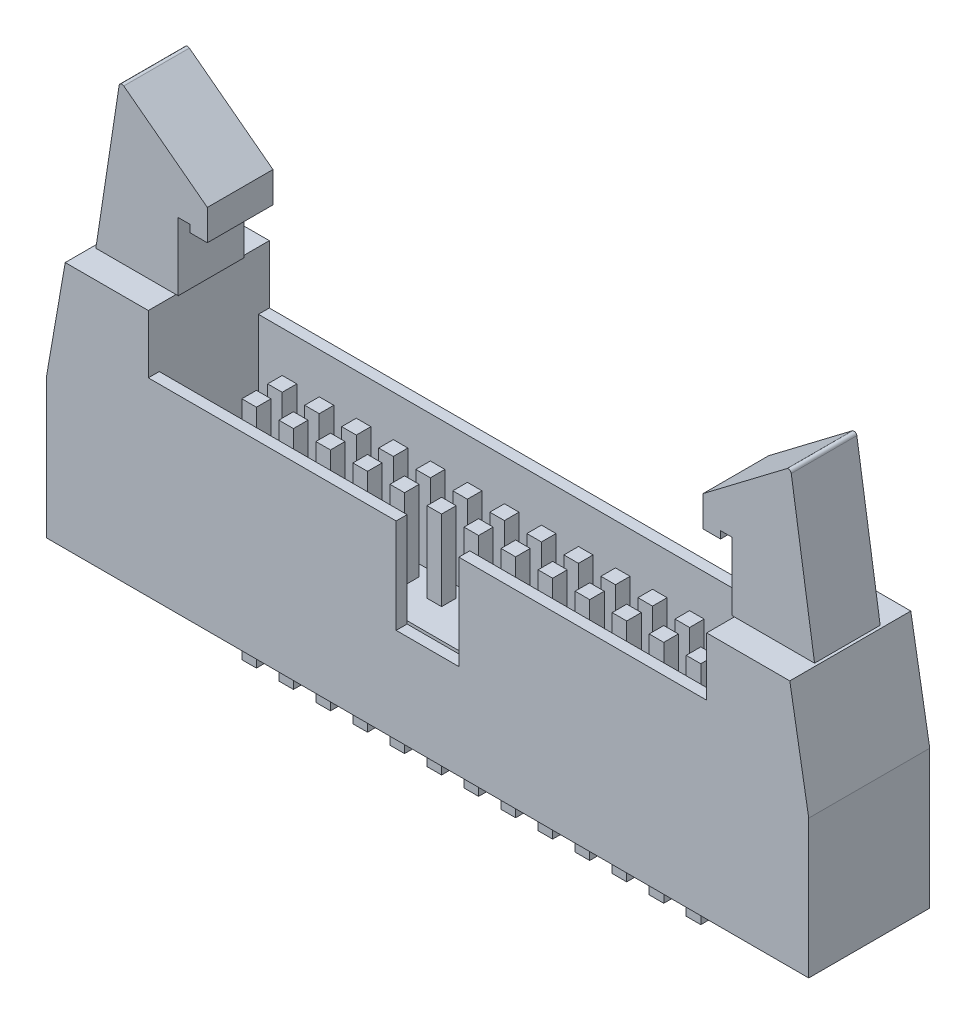
SolidWorks part; units mm, degrees
ref_plane "前视基准面" through (0, 0, 0) normal (0, 0, 1) x (1, 0, 0)
ref_plane "上视基准面" through (0, 0, 0) normal (0, 1, 0) x (1, 0, 0)
ref_plane "右视基准面" through (0, 0, 0) normal (1, 0, 0) x (0, 0, -1)
sketch "草图1" plane through (0, 0, 0) normal (0, 0, 1) x (1, 0, 0)
  line L0 (0, 0) -> (26960.7797, 0) construction
  line L1 (0, 0) -> (0, 26960.7797) construction
  line L2 (-26.15, 9.5) -> (-26.15, 0)
  line L3 (-26.15, 0) -> (26.15, 0)
  line L4 (26.15, 0) -> (26.15, 9.5)
  line L5 (26.15, 9.5) -> (24.85, 17)
  line L6 (24.85, 17) -> (19.15, 17)
  line L7 (19.15, 17) -> (19.15, 13)
  line L8 (-19.15, 17) -> (-19.15, 13)
  line L9 (-24.85, 17) -> (-19.15, 17)
  line L10 (-26.15, 9.5) -> (-24.85, 17)
  line L11 (-19.15, 13) -> (19.15, 13)
  dimension "D1" = 52.3
  dimension "D2" = 13
  dimension "D3" = 17
  dimension "D4" = 38.3
  dimension "D5" = 9.5
  dimension "D6" = 49.7
extrude "凸台-拉伸1" add sketch "草图1" along normal blind 8.3
sketch "草图2" plane through (0, 13, 0) normal (0, 1, 0) x (1, 0, 0)
  line L0 (-19.15, -8.3) -> (-19.15, 0) construction
  line L1 (-19.15, -0.75) -> (19.15, -0.75)
  line L2 (-19.15, -0.75) -> (-19.15, -7.55)
  line L3 (-19.15, -7.55) -> (19.15, -7.55)
  line L4 (19.15, -0.75) -> (19.15, -7.55)
  line L5 (19.15, -8.3) -> (19.15, 0) construction
  line L6 (19.15, 0) -> (-19.15, 0) construction
  line L7 (19.15, -8.3) -> (-19.15, -8.3) construction
  dimension "D1" = 0.75
  dimension "D2" = 0.75
extrude "切除-拉伸1" cut sketch "草图2" against normal blind 6.3
sketch "草图3" plane through (0, 0, 8.3) normal (0, 0, 1) x (1, 0, 0)
  line L0 (0, 0) -> (0, 50000) construction
  line L1 (19.15, 13) -> (-19.15, 13) construction
  line L2 (-2.15, 13) -> (2.15, 13)
  line L3 (-2.15, 13) -> (-2.15, 6.5)
  line L4 (-2.15, 6.5) -> (2.15, 6.5)
  line L5 (2.15, 13) -> (2.15, 6.5)
  dimension "D1" = 4.3
  dimension "D2" = 6.5
extrude "切除-拉伸2" cut sketch "草图3" against normal blind 0.75
ref_plane "基准面1" through (0, 0, 1.9) normal (0, 0, -1) x (-1, 0, 0)
sketch "草图4" plane through (0, 0, 1.9) normal (0, 0, -1) x (-1, 0, 0)
  line L0 (0, 0) -> (0, 50000) construction
  line L1 (-24.65, 17) -> (-23.0508, 27.4678)
  line L2 (-24.85, 17) -> (-19.15, 17) construction
  line L3 (-22.7322, 27.5969) -> (-17, 23.25)
  line L4 (-17, 23.25) -> (-17, 21.15)
  line L5 (-17, 21.15) -> (-18.2, 21.15)
  line L6 (-18.2, 21.15) -> (-18.2, 21.65)
  line L7 (-18.2, 21.65) -> (-19, 21.65)
  line L8 (-19, 21.65) -> (-19, 17)
  line L9 (-19, 17) -> (-24.65, 17)
  line L10 (-19.15, 13) -> (-2.15, 13) construction
  line L11 (26.15, 0) -> (-26.15, 0) construction
  line L13 (19, 17) -> (24.65, 17)
  line L14 (19, 21.65) -> (19, 17)
  line L15 (18.2, 21.65) -> (19, 21.65)
  line L16 (18.2, 21.15) -> (18.2, 21.65)
  line L17 (17, 21.15) -> (18.2, 21.15)
  line L18 (17, 23.25) -> (17, 21.15)
  line L19 (22.7322, 27.5969) -> (17, 23.25)
  line L20 (24.65, 17) -> (23.0508, 27.4678)
  arc A0 (-23.0508, 27.4678) -> (-22.7322, 27.5969) centre (-22.8531, 27.4376) cw
  arc A1 (23.0508, 27.4678) -> (22.7322, 27.5969) centre (22.8531, 27.4376) ccw
  point P21 (-23, 27.8)
  point P32 (23, 27.8)
  dimension "D10" = 0.2
  dimension "D1" = 8.15
  dimension "D2" = 27.8
  dimension "D3" = 23
  dimension "D4" = 17
  dimension "D5" = 2.1
  dimension "D6" = 1.2
  dimension "D7" = 0.5
  dimension "D8" = 19
  dimension "D9" = 0.2
extrude "凸台-拉伸2" add sketch "草图4" against normal blind 4.5
sketch "草图6" plane through (0, 6.7, 0) normal (0, 1, 0) x (1, 0, 0)
  line L0 (0, 0) -> (0, 50000) construction
  line L1 (8.36, -3.765) -> (8.36, -2.765)
  line L2 (0, -4.15) -> (50000, -4.15) construction
  line L3 (-15.5, -4.535) -> (-14.5, -4.535)
  line L4 (-15.5, -4.535) -> (-15.5, -5.535)
  line L5 (-15.5, -5.535) -> (-14.5, -5.535)
  line L6 (-14.5, -4.535) -> (-14.5, -5.535)
  line L7 (19.15, -8.3) -> (2.15, -8.3) construction
  line L8 (19.15, 0) -> (-19.15, 0) construction
  line L9 (7.36, -2.765) -> (8.36, -2.765)
  line L10 (-12.96, -4.535) -> (-11.96, -4.535)
  line L11 (-12.96, -4.535) -> (-12.96, -5.535)
  line L12 (-12.96, -5.535) -> (-11.96, -5.535)
  line L13 (-11.96, -4.535) -> (-11.96, -5.535)
  line L14 (-10.42, -4.535) -> (-9.42, -4.535)
  line L15 (-10.42, -4.535) -> (-10.42, -5.535)
  line L16 (-10.42, -5.535) -> (-9.42, -5.535)
  line L17 (-9.42, -4.535) -> (-9.42, -5.535)
  line L18 (-7.88, -4.535) -> (-6.88, -4.535)
  line L19 (-7.88, -4.535) -> (-7.88, -5.535)
  line L20 (-7.88, -5.535) -> (-6.88, -5.535)
  line L21 (-6.88, -4.535) -> (-6.88, -5.535)
  line L22 (-5.34, -4.535) -> (-4.34, -4.535)
  line L23 (-5.34, -4.535) -> (-5.34, -5.535)
  line L24 (-5.34, -5.535) -> (-4.34, -5.535)
  line L25 (-4.34, -4.535) -> (-4.34, -5.535)
  line L26 (-2.8, -4.535) -> (-1.8, -4.535)
  line L27 (-2.8, -4.535) -> (-2.8, -5.535)
  line L28 (-2.8, -5.535) -> (-1.8, -5.535)
  line L29 (-1.8, -4.535) -> (-1.8, -5.535)
  line L30 (-0.26, -4.535) -> (0.74, -4.535)
  line L31 (-0.26, -4.535) -> (-0.26, -5.535)
  line L32 (-0.26, -5.535) -> (0.74, -5.535)
  line L33 (0.74, -4.535) -> (0.74, -5.535)
  line L34 (2.28, -4.535) -> (3.28, -4.535)
  line L35 (2.28, -4.535) -> (2.28, -5.535)
  line L36 (2.28, -5.535) -> (3.28, -5.535)
  line L37 (3.28, -4.535) -> (3.28, -5.535)
  line L38 (4.82, -4.535) -> (5.82, -4.535)
  line L39 (4.82, -4.535) -> (4.82, -5.535)
  line L40 (4.82, -5.535) -> (5.82, -5.535)
  line L41 (5.82, -4.535) -> (5.82, -5.535)
  line L42 (7.36, -4.535) -> (8.36, -4.535)
  line L43 (7.36, -4.535) -> (7.36, -5.535)
  line L44 (7.36, -5.535) -> (8.36, -5.535)
  line L45 (8.36, -4.535) -> (8.36, -5.535)
  line L46 (7.36, -3.765) -> (7.36, -2.765)
  line L47 (7.36, -3.765) -> (8.36, -3.765)
  line L48 (5.82, -3.765) -> (5.82, -2.765)
  line L49 (4.82, -2.765) -> (5.82, -2.765)
  line L50 (4.82, -3.765) -> (4.82, -2.765)
  line L51 (4.82, -3.765) -> (5.82, -3.765)
  line L52 (3.28, -3.765) -> (3.28, -2.765)
  line L53 (2.28, -2.765) -> (3.28, -2.765)
  line L54 (2.28, -3.765) -> (2.28, -2.765)
  line L55 (2.28, -3.765) -> (3.28, -3.765)
  line L56 (0.74, -3.765) -> (0.74, -2.765)
  line L57 (-0.26, -2.765) -> (0.74, -2.765)
  line L58 (-0.26, -3.765) -> (-0.26, -2.765)
  line L59 (-0.26, -3.765) -> (0.74, -3.765)
  line L60 (-1.8, -3.765) -> (-1.8, -2.765)
  line L61 (-2.8, -2.765) -> (-1.8, -2.765)
  line L62 (-2.8, -3.765) -> (-2.8, -2.765)
  line L63 (-2.8, -3.765) -> (-1.8, -3.765)
  line L64 (-4.34, -3.765) -> (-4.34, -2.765)
  line L65 (-5.34, -2.765) -> (-4.34, -2.765)
  line L66 (-5.34, -3.765) -> (-5.34, -2.765)
  line L67 (-5.34, -3.765) -> (-4.34, -3.765)
  line L68 (-6.88, -3.765) -> (-6.88, -2.765)
  line L69 (-7.88, -2.765) -> (-6.88, -2.765)
  line L70 (-7.88, -3.765) -> (-7.88, -2.765)
  line L71 (-7.88, -3.765) -> (-6.88, -3.765)
  line L72 (-9.42, -3.765) -> (-9.42, -2.765)
  line L73 (-10.42, -2.765) -> (-9.42, -2.765)
  line L74 (-10.42, -3.765) -> (-10.42, -2.765)
  line L75 (-10.42, -3.765) -> (-9.42, -3.765)
  line L76 (-11.96, -3.765) -> (-11.96, -2.765)
  line L77 (-12.96, -2.765) -> (-11.96, -2.765)
  line L78 (-12.96, -3.765) -> (-12.96, -2.765)
  line L79 (-12.96, -3.765) -> (-11.96, -3.765)
  line L80 (-14.5, -3.765) -> (-14.5, -2.765)
  line L81 (-15.5, -2.765) -> (-14.5, -2.765)
  line L82 (-15.5, -3.765) -> (-15.5, -2.765)
  line L83 (-15.5, -3.765) -> (-14.5, -3.765)
  line L84 (9.9, -4.535) -> (10.9, -4.535)
  line L85 (9.9, -4.535) -> (9.9, -5.535)
  line L86 (9.9, -5.535) -> (10.9, -5.535)
  line L87 (10.9, -4.535) -> (10.9, -5.535)
  line L88 (12.44, -4.535) -> (13.44, -4.535)
  line L89 (12.44, -4.535) -> (12.44, -5.535)
  line L90 (12.44, -5.535) -> (13.44, -5.535)
  line L91 (13.44, -4.535) -> (13.44, -5.535)
  line L92 (14.98, -4.535) -> (15.98, -4.535)
  line L93 (14.98, -4.535) -> (14.98, -5.535)
  line L94 (14.98, -5.535) -> (15.98, -5.535)
  line L95 (15.98, -4.535) -> (15.98, -5.535)
  line L96 (10.9, -3.765) -> (10.9, -2.765)
  line L97 (9.9, -2.765) -> (10.9, -2.765)
  line L98 (9.9, -3.765) -> (9.9, -2.765)
  line L99 (9.9, -3.765) -> (10.9, -3.765)
  line L100 (13.44, -3.765) -> (13.44, -2.765)
  line L101 (12.44, -2.765) -> (13.44, -2.765)
  line L102 (12.44, -3.765) -> (12.44, -2.765)
  line L103 (12.44, -3.765) -> (13.44, -3.765)
  line L104 (15.98, -3.765) -> (15.98, -2.765)
  line L105 (14.98, -2.765) -> (15.98, -2.765)
  line L106 (14.98, -3.765) -> (14.98, -2.765)
  line L107 (14.98, -3.765) -> (15.98, -3.765)
  dimension "D1" = 1
  dimension "D2" = 1
  dimension "D3" = 15.5
  dimension "D4" = 0.77
  dimension "D5" = 13
  dimension "D6" = 4
extrude "凸台-拉伸3" add sketch "草图6" along normal blind 5.5 and the other way blind 10
